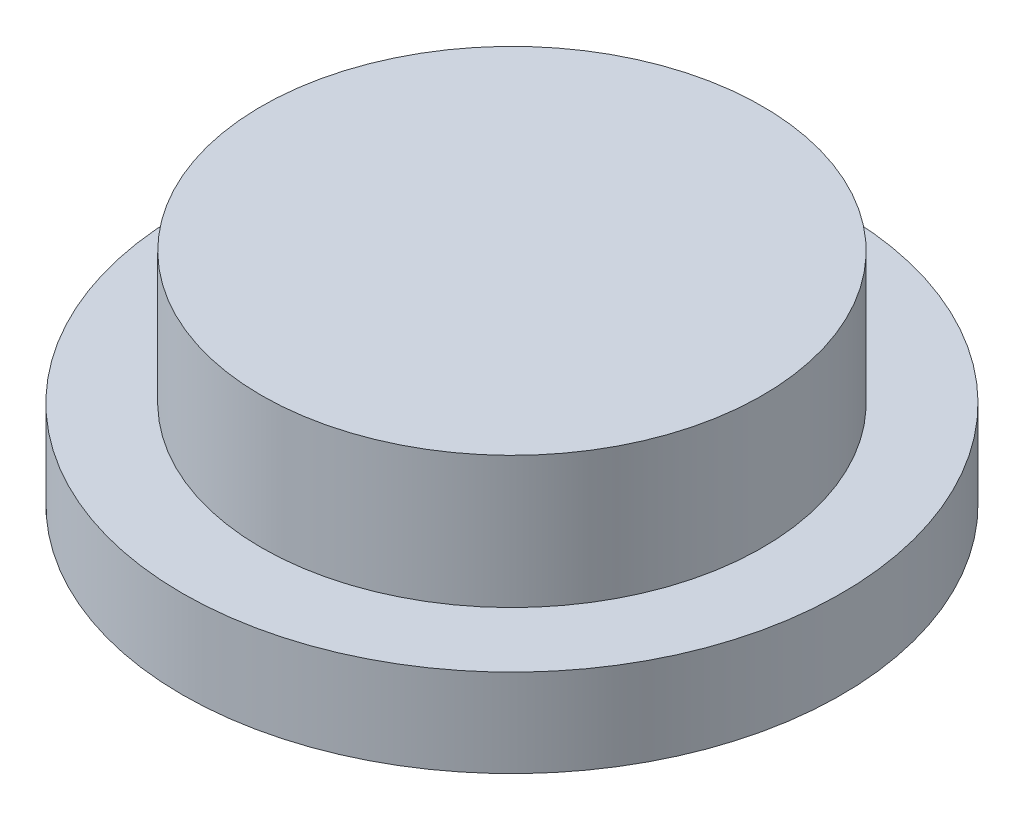
SolidWorks part; units mm, degrees
ref_plane "Front Plane" through (0, 0, 0) normal (0, 0, 1) x (1, 0, 0)
ref_plane "Top Plane" through (0, 0, 0) normal (0, 1, 0) x (1, 0, 0)
ref_plane "Right Plane" through (0, 0, 0) normal (1, 0, 0) x (0, 0, -1)
sketch "Sketch1" plane through (0, 0, 0) normal (0, 1, 0) x (1, 0, 0)
  circle A0 centre (0, 0) radius 7.5
  dimension "D1" = 15
extrude "Boss-Extrude1" add sketch "Sketch1" along normal blind 2
sketch "Sketch2" plane through (0, 2, 0) normal (0, 1, 0) x (1, 0, 0)
  circle A0 centre (0, 0) radius 5.7
  dimension "D1" = 11.4
extrude "Boss-Extrude2" add sketch "Sketch2" along normal blind 3
